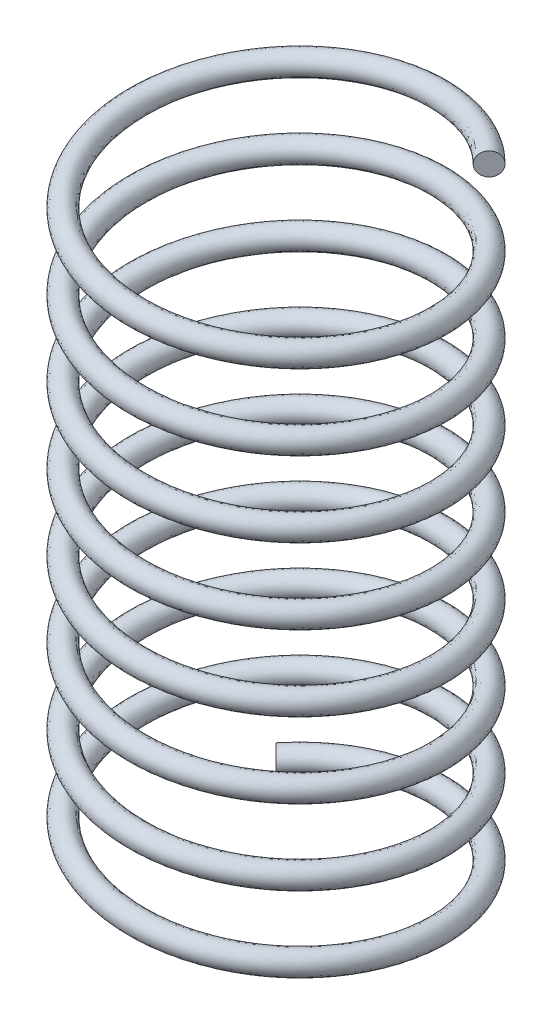
SolidWorks part; units mm, degrees
ref_plane "Front Plane" through (0, 0, 0) normal (0, 0, 1) x (1, 0, 0)
ref_plane "Top Plane" through (0, 0, 0) normal (0, 1, 0) x (1, 0, 0)
ref_plane "Right Plane" through (0, 0, 0) normal (1, 0, 0) x (0, 0, -1)
sketch "Sketch1" plane through (0, 0, 0) normal (0, 1, 0) x (1, 0, 0)
  circle A0 centre (0, 0) radius 40
  dimension "D1" = 80
curve "Helix/Spiral1" pitch 20 height 165 turns 8.25
sketch "Sketch2" plane through (0, 0, 0) normal (0, 0, 1) x (1, 0, 0)
  circle A0 centre (-39.9997, 77.5) radius 3
  spline S0 degree 3 poles (-28.2843, 0) (-26.173, 0.2376) (-21.4586, 0.7145) (-13.323, 1.4285) (-4.5162, 2.1429) (4.5163, 2.8571) (13.3225, 3.5714) (21.4606, 4.2857) (28.5226, 5) (34.1544, 5.7143) (38.0735, 6.4286) (40.0835, 7.1429) (40.0835, 7.8571) (38.0735, 8.5714) (34.1544, 9.2857) (28.5226, 10) (21.4606, 10.7143) (13.3225, 11.4286) (4.5163, 12.1429) (-4.5163, 12.8571) (-13.3225, 13.5714) (-21.4606, 14.2857) (-28.5226, 15) (-34.1544, 15.7143) (-38.0735, 16.4286) (-40.0835, 17.1429) (-40.0835, 17.8571) (-38.0735, 18.5714) (-34.1544, 19.2857) (-28.5226, 20) (-21.4606, 20.7143) (-13.3225, 21.4286) (-4.5163, 22.1429) (4.5163, 22.8571) (13.3225, 23.5714) (21.4606, 24.2857) (28.5226, 25) (34.1544, 25.7143) (38.0735, 26.4286) (40.0835, 27.1429) (40.0835, 27.8571) (38.0735, 28.5714) (34.1544, 29.2857) (28.5226, 30) (21.4606, 30.7143) (13.3225, 31.4286) (4.5163, 32.1429) (-4.5163, 32.8571) (-13.3225, 33.5714) (-21.4606, 34.2857) (-28.5226, 35) (-34.1544, 35.7143) (-38.0735, 36.4286) (-40.0835, 37.1429) (-40.0835, 37.8571) (-38.0735, 38.5714) (-34.1544, 39.2857) (-28.5226, 40) (-21.4606, 40.7143) (-13.3225, 41.4286) (-4.5163, 42.1429) (4.5163, 42.8571) (13.3225, 43.5714) (21.4606, 44.2857) (28.5226, 45) (34.1544, 45.7143) (38.0735, 46.4286) (40.0835, 47.1429) (40.0835, 47.8571) (38.0735, 48.5714) (34.1544, 49.2857) (28.5226, 50) (21.4606, 50.7143) (13.3225, 51.4286) (4.5163, 52.1429) (-4.5163, 52.8571) (-13.3225, 53.5714) (-21.4606, 54.2857) (-28.5226, 55) (-34.1544, 55.7143) (-38.0735, 56.4286) (-40.0835, 57.1429) (-40.0835, 57.8571) (-38.0735, 58.5714) (-34.1544, 59.2857) (-28.5226, 60) (-21.4606, 60.7143) (-13.3225, 61.4286) (-4.5163, 62.1429) (4.5163, 62.8571) (13.3225, 63.5714) (21.4606, 64.2857) (28.5226, 65) (34.1544, 65.7143) (38.0735, 66.4286) (40.0835, 67.1429) (40.0835, 67.8571) (38.0735, 68.5714) (34.1544, 69.2857) (28.5226, 70) (21.4606, 70.7143) (13.3225, 71.4286) (4.5163, 72.1429) (-4.5163, 72.8571) (-13.3225, 73.5714) (-21.4606, 74.2857) (-28.5226, 75) (-34.1544, 75.7143) (-38.0735, 76.4286) (-40.0835, 77.1429) (-40.0835, 77.8571) (-38.0735, 78.5714) (-34.1544, 79.2857) (-28.5226, 80) (-21.4606, 80.7143) (-13.3225, 81.4286) (-4.5163, 82.1429) (4.5163, 82.8571) (13.3225, 83.5714) (21.4606, 84.2857) (28.5226, 85) (34.1544, 85.7143) (38.0735, 86.4286) (40.0835, 87.1429) (40.0835, 87.8571) (38.0735, 88.5714) (34.1544, 89.2857) (28.5226, 90) (21.4606, 90.7143) (13.3225, 91.4286) (4.5163, 92.1429) (-4.5163, 92.8571) (-13.3225, 93.5714) (-21.4606, 94.2857) (-28.5226, 95) (-34.1544, 95.7143) (-38.0735, 96.4286) (-40.0835, 97.1429) (-40.0835, 97.8571) (-38.0735, 98.5714) (-34.1544, 99.2857) (-28.5226, 100) (-21.4606, 100.7143) (-13.3225, 101.4286) (-4.5163, 102.1429) (4.5163, 102.8571) (13.3225, 103.5714) (21.4606, 104.2857) (28.5226, 105) (34.1544, 105.7143) (38.0735, 106.4286) (40.0835, 107.1429) (40.0835, 107.8571) (38.0735, 108.5714) (34.1544, 109.2857) (28.5226, 110) (21.4606, 110.7143) (13.3225, 111.4286) (4.5163, 112.1429) (-4.5163, 112.8571) (-13.3225, 113.5714) (-21.4606, 114.2857) (-28.5226, 115) (-34.1544, 115.7143) (-38.0735, 116.4286) (-40.0835, 117.1429) (-40.0835, 117.8571) (-38.0735, 118.5714) (-34.1544, 119.2857) (-28.5226, 120) (-21.4606, 120.7143) (-13.3225, 121.4286) (-4.5163, 122.1429) (4.5163, 122.8571) (13.3225, 123.5714) (21.4606, 124.2857) (28.5226, 125) (34.1544, 125.7143) (38.0735, 126.4286) (40.0835, 127.1429) (40.0835, 127.8571) (38.0735, 128.5714) (34.1544, 129.2857) (28.5226, 130) (21.4606, 130.7143) (13.3225, 131.4286) (4.5163, 132.1429) (-4.5163, 132.8571) (-13.3225, 133.5714) (-21.4606, 134.2857) (-28.5226, 135) (-34.1544, 135.7143) (-38.0735, 136.4286) (-40.0835, 137.1429) (-40.0835, 137.8571) (-38.0735, 138.5714) (-34.1544, 139.2857) (-28.5226, 140) (-21.4606, 140.7143) (-13.3225, 141.4286) (-4.5163, 142.1429) (4.5163, 142.8571) (13.3225, 143.5714) (21.4606, 144.2857) (28.5226, 145) (34.1544, 145.7143) (38.0735, 146.4286) (40.0835, 147.1429) (40.0835, 147.8571) (38.0735, 148.5714) (34.1544, 149.2857) (28.5226, 150) (21.4606, 150.7143) (13.3225, 151.4286) (4.5163, 152.1429) (-4.5163, 152.8571) (-13.3225, 153.5714) (-21.4606, 154.2857) (-28.5226, 155) (-34.1544, 155.7143) (-38.0735, 156.4286) (-40.0835, 157.1429) (-40.0835, 157.8571) (-38.0735, 158.5714) (-34.1544, 159.2857) (-28.5226, 160) (-21.4606, 160.7143) (-13.3225, 161.4286) (-4.5163, 162.1429) (4.5162, 162.8571) (13.323, 163.5715) (21.4586, 164.2855) (26.173, 164.7624) (28.2843, 165) knots 0 0 0 0 0.004329 0.008658 0.012987 0.017316 0.021645 0.025974 0.030303 0.034632 0.038961 0.04329 0.047619 0.051948 0.056277 0.060606 0.064935 0.069264 0.073593 0.077922 0.082251 0.08658 0.090909 0.095238 0.099567 0.103896 0.108225 0.112554 0.116883 0.121212 0.125541 0.12987 0.134199 0.138528 0.142857 0.147186 0.151515 0.155844 0.160173 0.164502 0.168831 0.17316 0.177489 0.181818 0.186147 0.190476 0.194805 0.199134 0.203463 0.207792 0.212121 0.21645 0.220779 0.225108 0.229437 0.233766 0.238095 0.242424 0.246753 0.251082 0.255411 0.25974 0.264069 0.268398 0.272727 0.277056 0.281385 0.285714 0.290043 0.294372 0.298701 0.30303 0.307359 0.311688 0.316017 0.320346 0.324675 0.329004 0.333333 0.337662 0.341991 0.34632 0.350649 0.354978 0.359307 0.363636 0.367965 0.372294 0.376623 0.380952 0.385281 0.38961 0.393939 0.398268 0.402597 0.406926 0.411255 0.415584 0.419913 0.424242 0.428571 0.4329 0.437229 0.441558 0.445887 0.450216 0.454545 0.458874 0.463203 0.467532 0.471861 0.47619 0.480519 0.484848 0.489177 0.493506 0.497835 0.502165 0.506494 0.510823 0.515152 0.519481 0.52381 0.528139 0.532468 0.536797 0.541126 0.545455 0.549784 0.554113 0.558442 0.562771 0.5671 0.571429 0.575758 0.580087 0.584416 0.588745 0.593074 0.597403 0.601732 0.606061 0.61039 0.614719 0.619048 0.623377 0.627706 0.632035 0.636364 0.640693 0.645022 0.649351 0.65368 0.658009 0.662338 0.666667 0.670996 0.675325 0.679654 0.683983 0.688312 0.692641 0.69697 0.701299 0.705628 0.709957 0.714286 0.718615 0.722944 0.727273 0.731602 0.735931 0.74026 0.744589 0.748918 0.753247 0.757576 0.761905 0.766234 0.770563 0.774892 0.779221 0.78355 0.787879 0.792208 0.796537 0.800866 0.805195 0.809524 0.813853 0.818182 0.822511 0.82684 0.831169 0.835498 0.839827 0.844156 0.848485 0.852814 0.857143 0.861472 0.865801 0.87013 0.874459 0.878788 0.883117 0.887446 0.891775 0.896104 0.900433 0.904762 0.909091 0.91342 0.917749 0.922078 0.926407 0.930736 0.935065 0.939394 0.943723 0.948052 0.952381 0.95671 0.961039 0.965368 0.969697 0.974026 0.978355 0.982684 0.987013 0.991342 0.995671 1 1 1 1 construction
  dimension "D1" = 6
sweep "Sweep1" add profiles "Sketch2" path "Helix/Spiral1"
